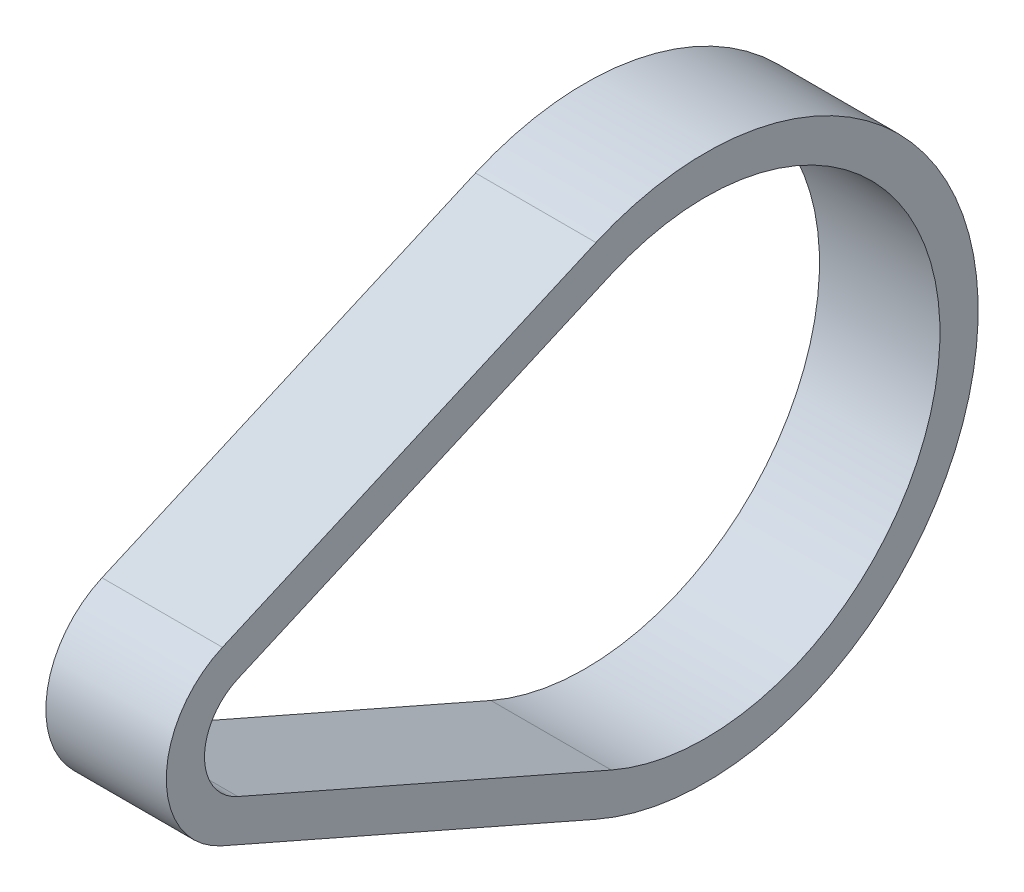
SolidWorks part; units mm, degrees
ref_plane "Front Plane" through (0, 0, 0) normal (0, 0, 1) x (1, 0, 0)
ref_plane "Top Plane" through (0, 0, 0) normal (0, 1, 0) x (1, 0, 0)
ref_plane "Right Plane" through (0, 0, 0) normal (1, 0, 0) x (0, 0, -1)
other "Bounding Box"
ref_plane "Default Plane" through (-8.9266, -12.7485, 0) normal (-0.1736, 0.9848, 0) x (0.9848, 0.1736, 0)
sketch "Sketch1" plane through (0, 0, 0) normal (1, 0, 0) x (0, 0, -1)
  line L0 (0, 0) -> (55.4609, 0) construction
  line L1 (-2.7817, 6.3435) -> (43.7342, 26.7416)
  line L2 (-2.7817, -6.3435) -> (43.7342, -26.7416)
  line L3 (-4.6944, 10.705) -> (41.8215, 31.1032)
  line L4 (-4.6944, -10.705) -> (41.8215, -31.1032)
  line L5 (-6.9266, 0) -> (-11.6891, 0) construction
  line L6 (84.6607, 0) -> (89.4232, 0) construction
  arc A0 (-2.7817, 6.3435) -> (-2.7817, -6.3435) centre (0, 0) ccw
  arc A1 (43.7342, -26.7416) -> (43.7342, 26.7416) centre (55.4609, 0) ccw
  arc A2 (-4.6944, 10.705) -> (-4.6944, -10.705) centre (0, 0) ccw
  arc A3 (41.8215, -31.1032) -> (41.8215, 31.1032) centre (55.4609, 0) ccw
  dimension "D2" = 4.7625
  dimension "D4" = 13.8532
  dimension "D5" = 58.3997
  dimension "D1" = 55.4609
extrude "Boss-Extrude1" add sketch "Sketch1" along normal mid plane 15
